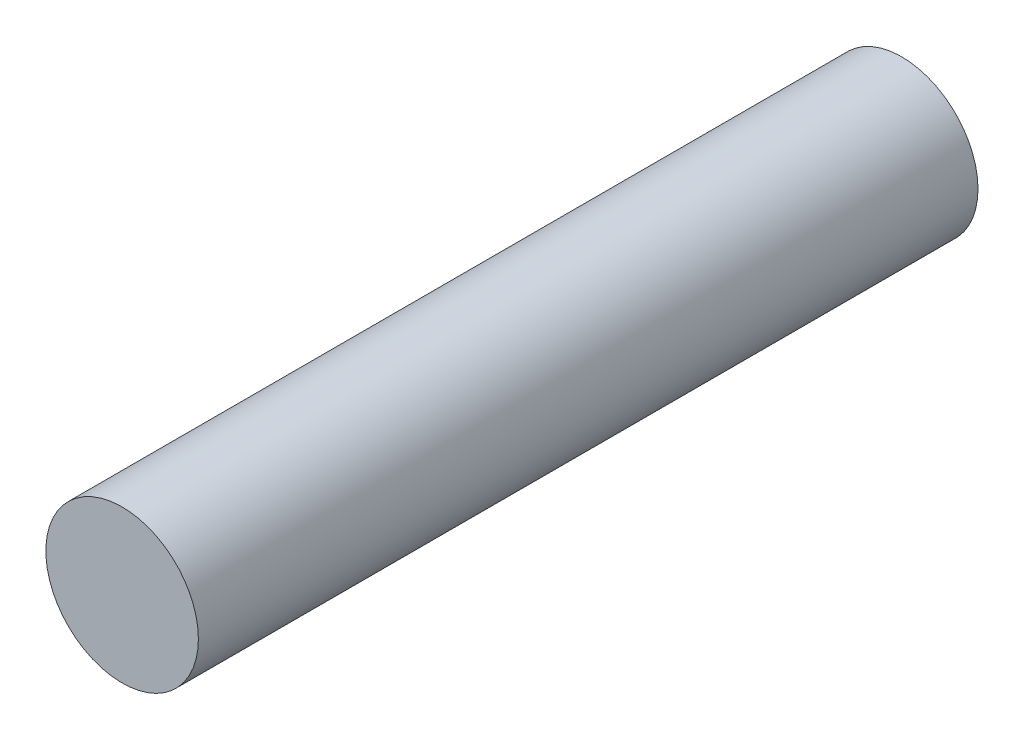
SolidWorks part; units mm, degrees
ref_plane "Front Plane" through (0, 0, 0) normal (0, 0, 1) x (1, 0, 0)
ref_plane "Top Plane" through (0, 0, 0) normal (0, 1, 0) x (1, 0, 0)
ref_plane "Right Plane" through (0, 0, 0) normal (1, 0, 0) x (0, 0, -1)
sketch "草图1" plane through (0, 0, 0) normal (0, 0, 1) x (1, 0, 0)
  circle A0 centre (0, 0) radius 2.25
  dimension "D1" = 4.5
extrude "凸台-拉伸2" add sketch "草图1" along normal blind 23
sketch "草图7" plane through (0, 0, 0) normal (0, 0, 1) x (1, 0, 0)
  line L1 (1.175, -1.175) -> (-1.175, -1.175)
  line L2 (1.175, -1.175) -> (1.175, 1.175)
  line L3 (1.175, 1.175) -> (-1.175, 1.175)
  line L4 (-1.175, -1.175) -> (-1.175, 1.175)
  line L5 (1.175, -1.175) -> (-1.175, 1.175) construction
  line L6 (1.175, 1.175) -> (-1.175, -1.175) construction
  point P0 (0, 0)
  dimension "D1" = 2.35
  dimension "D2" = 2.35
extrude "切除-拉伸3" cut sketch "草图7" along normal blind 4.5 from surface at 0 starting at face at (2.25, 0, 0)
